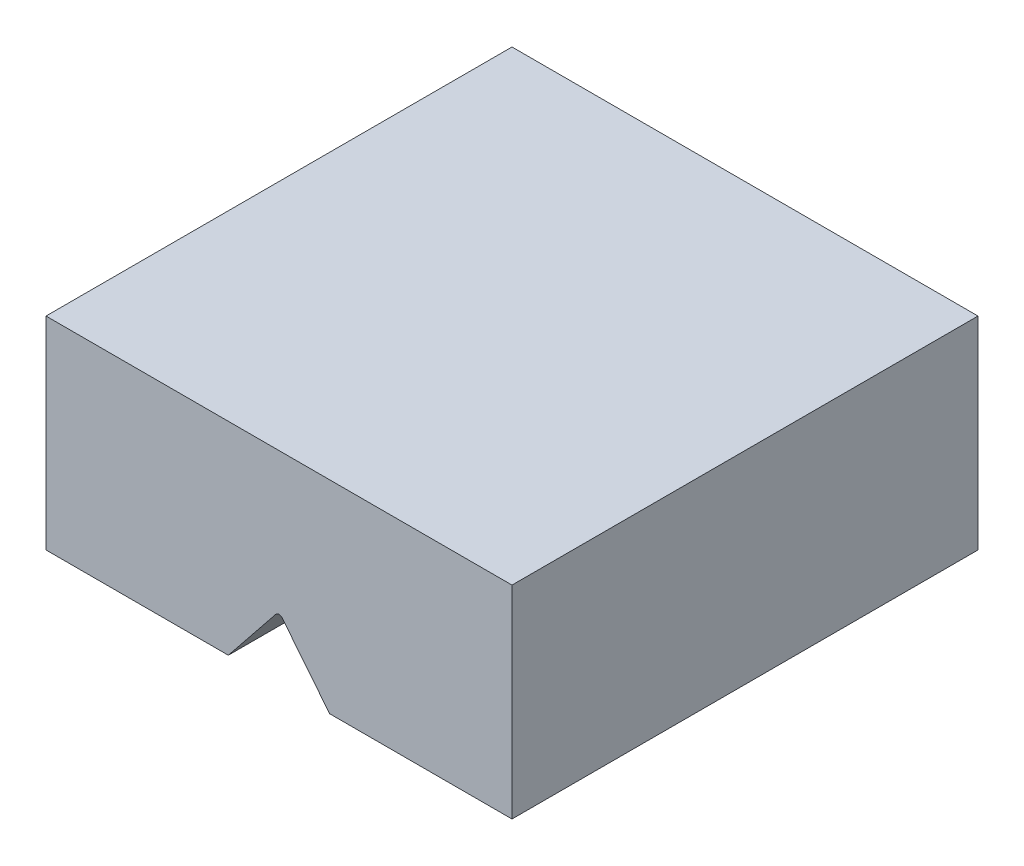
SolidWorks part; units mm, degrees
ref_plane "Front Plane" through (0, 0, 0) normal (0, 0, 1) x (1, 0, 0)
ref_plane "Top Plane" through (0, 0, 0) normal (0, 1, 0) x (1, 0, 0)
ref_plane "Right Plane" through (0, 0, 0) normal (1, 0, 0) x (0, 0, -1)
sketch "Sketch1" plane through (0, 0, 0) normal (0, 1, 0) x (1, 0, 0)
  line L0 (-11.5, -11.5) -> (11.5, 11.5) construction
  line L1 (-11.5, -11.5) -> (11.5, -11.5)
  line L2 (-11.5, -11.5) -> (-11.5, 11.5)
  line L3 (-11.5, 11.5) -> (11.5, 11.5)
  line L4 (11.5, -11.5) -> (11.5, 11.5)
  dimension "D1" = 23
extrude "Boss-Extrude1" add sketch "Sketch1" along normal blind 10
sketch "Sketch2" plane through (0, 0, 11.5) normal (0, 0, 1) x (1, 0, 0)
  line L0 (-2.5, 0) -> (-0.1561, 2.9251)
  line L1 (-11.5, 0) -> (11.5, 0) construction
  line L2 (0.1561, 2.9251) -> (2.5, 0)
  line L3 (-2.5, 0) -> (2.5, 0)
  arc A0 (-0.1561, 2.9251) -> (0.1561, 2.9251) centre (0, 2.8) cw
  dimension "D1" = 0.2
  dimension "D3" = 5
  dimension "D2" = 3
extrude "Cut-Extrude1" cut sketch "Sketch2" against normal through all
sketch "Sketch3" plane through (0, 0, 0) normal (0, -1, 0) x (1, 0, 0)
  circle A0 centre (0, 0) radius 2.2
  dimension "D1" = 4.4
extrude "Cut-Extrude2" cut sketch "Sketch3" against normal blind 5.3
